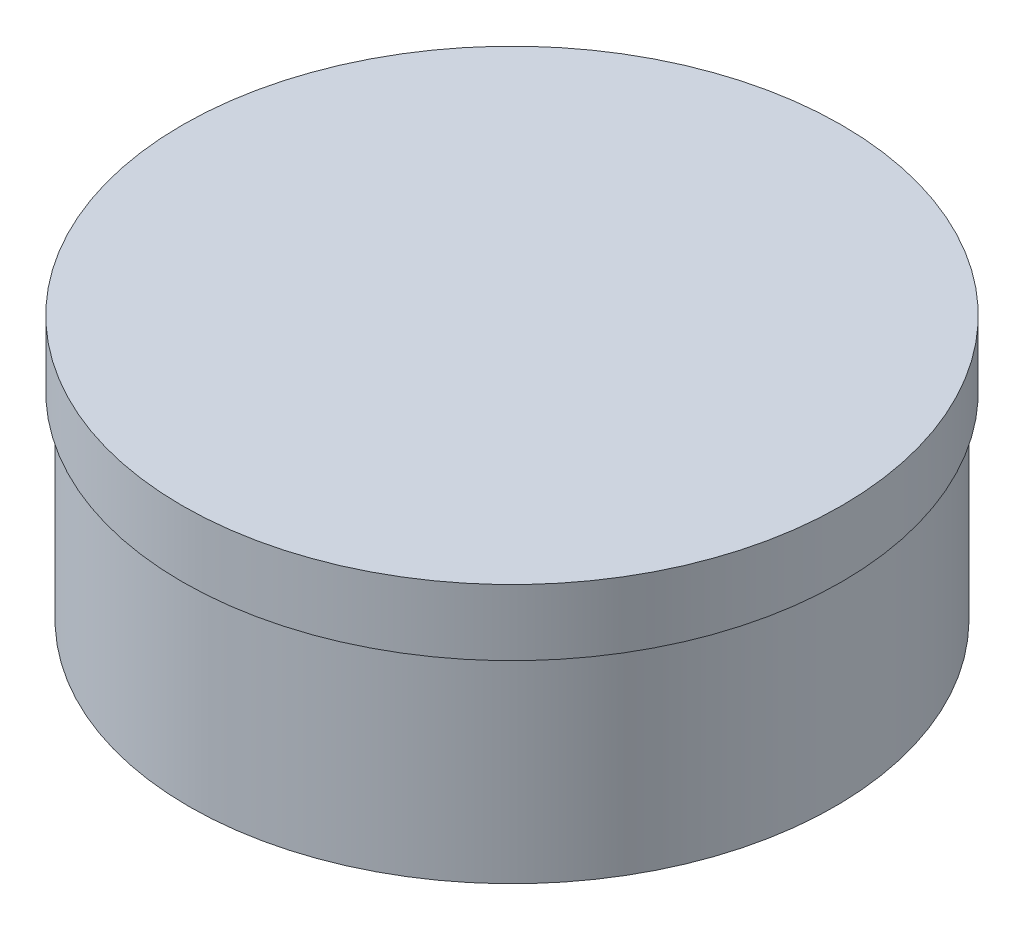
SolidWorks part; units mm, degrees
material "ABS"
ref_plane "Front Plane" through (0, 0, 0) normal (0, 0, 1) x (1, 0, 0)
ref_plane "Top Plane" through (0, 0, 0) normal (0, 1, 0) x (1, 0, 0)
ref_plane "Right Plane" through (0, 0, 0) normal (1, 0, 0) x (0, 0, -1)
sketch "Sketch1" plane through (0, 0, 0) normal (0, 1, 0) x (1, 0, 0)
  circle A0 centre (0, 0) radius 4.9
  circle A1 centre (0, 0) radius 3.8
  dimension "D1" = 7.6
  dimension "D2" = 9.8
extrude "Boss-Extrude1" add sketch "Sketch1" along normal blind 3
sketch "Sketch2" plane through (0, 3, 0) normal (0, 1, 0) x (1, 0, 0)
  circle A0 centre (0, 0) radius 5
  dimension "D1" = 10
extrude "Boss-Extrude2" add sketch "Sketch2" along normal blind 1
chamfer "Chamfer1" distance 0.5 angle 45 1 edges at (0, 0, 3.8)
